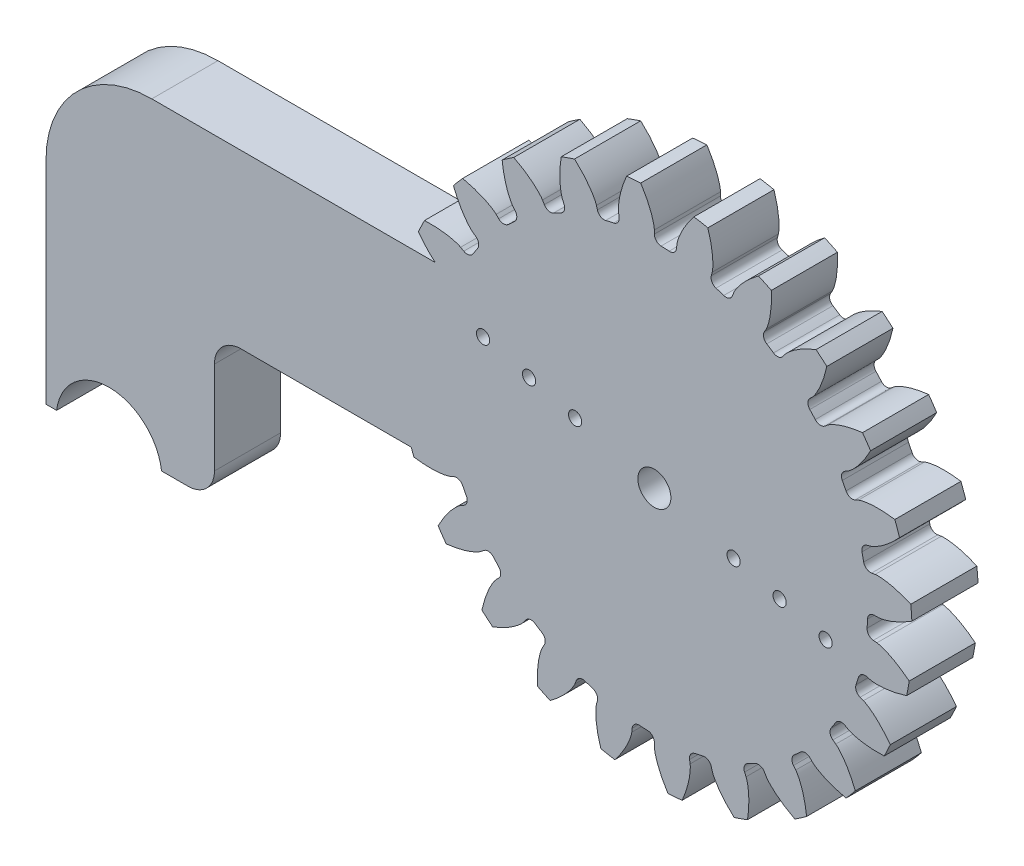
SolidWorks part; units mm, degrees
other "标注1"
sketch "草图12" plane through (-30.0305, -39.4698, -2.5) normal (-0.0916, -0.3639, -0.9269) x (-0.8028, -0.5238, 0.285)
ref_plane "前视基准面" through (0, 0, 0) normal (0, 0, 1) x (1, 0, 0)
ref_plane "上视基准面" through (0, 0, 0) normal (0, 1, 0) x (1, 0, 0)
ref_plane "右视基准面" through (0, 0, 0) normal (1, 0, 0) x (0, 0, -1)
sketch "草图1" plane through (0, 0, 0) normal (0, 0, 1) x (1, 0, 0)
  circle A0 centre (0, 0) radius 19.5
  dimension "D1" = 39
extrude "凸台-拉伸1" add sketch "草图1" along normal mid plane 5
sketch "草图4" plane through (0, 0, 0) normal (0, 0, 1) x (1, 0, 0)
  line L1 (0, 0) -> (23.8901, -1.2086) construction
  line L2 (16.9145, 0) -> (16.125, 0)
  line L3 (16.8281, -1.707) -> (16.0427, -1.6273)
  arc A1 (17.998, 0.2683) -> (17.977, -0.9094) centre (0, 0) cw construction
  arc A3 (23.372, 5.0941) -> (22.7385, -7.4268) centre (0, 0) cw
  arc A4 (16.0427, -1.6273) -> (16.125, 0) centre (0, 0) ccw
  spline S0 degree 4 poles (16.8281, -1.707) (16.8405, -1.7085) (16.8752, -1.7136) (16.9404, -1.7264) (17.0458, -1.7519) (17.1786, -1.7908) (17.3482, -1.8487) (17.545, -1.9264) (17.7579, -2.0215) (17.9853, -2.1355) (18.2084, -2.2583) (18.4269, -2.3892) (18.6409, -2.527) (18.8954, -2.7025) (19.194, -2.9248) (19.5326, -3.2014) (19.9037, -3.5346) (20.2673, -3.8941) (20.6127, -4.264) (20.9467, -4.6555) (21.259, -5.0467) (21.567, -5.4702) (21.843, -5.8697) (22.1332, -6.3351) (22.3619, -6.716) (22.6425, -7.2361) (22.8019, -7.5485) (22.981, -7.9199) (23.0566, -8.0879) (23.1032, -8.1912) knots 0 0 0 0 0 0.005377 0.015084 0.028532 0.04661 0.064855 0.092111 0.119476 0.146842 0.174209 0.201575 0.228941 0.256307 0.307035 0.361767 0.4165 0.471232 0.525964 0.580697 0.635429 0.690161 0.744894 0.799626 0.854358 0.909091 0.954545 1 1 1 1 1 construction
  spline S1 degree 4 poles (16.8281, -1.707) (16.8405, -1.7085) (16.8752, -1.7136) (16.9404, -1.7264) (17.0458, -1.7519) (17.1786, -1.7908) (17.3482, -1.8487) (17.545, -1.9264) (17.7579, -2.0215) (17.9853, -2.1355) (18.2084, -2.2583) (18.4269, -2.3892) (18.6409, -2.527) (18.8954, -2.7025) (19.194, -2.9248) (19.5326, -3.2014) (19.9037, -3.5346) (20.2673, -3.8941) (20.6127, -4.264) (20.9467, -4.6555) (21.259, -5.0467) (21.567, -5.4702) (21.843, -5.8697) (22.1332, -6.3351) (22.3619, -6.716) (22.5816, -7.1233) (22.6862, -7.3236) (22.7386, -7.4268) knots 0 0 0 0 0 0.005377 0.015084 0.028532 0.04661 0.064855 0.092111 0.119476 0.146842 0.174209 0.201575 0.228941 0.256307 0.307035 0.361767 0.4165 0.471232 0.525964 0.580697 0.635429 0.690161 0.744894 0.799626 0.854358 0.909089 0.909089 0.909089 0.909089 0.909089
  spline S2 degree 4 poles (16.9145, 0) (16.927, 0.0003) (16.962, 0.0018) (17.0281, 0.008) (17.1356, 0.0227) (17.2716, 0.0481) (17.4462, 0.0885) (17.6498, 0.1459) (17.8712, 0.2191) (18.109, 0.3096) (18.3433, 0.4092) (18.5739, 0.5174) (18.8007, 0.6329) (19.0717, 0.7818) (19.3912, 0.9728) (19.7559, 1.2138) (20.1588, 1.5079) (20.5568, 1.8288) (20.9378, 2.162) (21.3096, 2.5178) (21.6598, 2.8755) (22.0089, 3.2657) (22.3239, 3.6354) (22.6595, 4.0691) (22.9254, 4.4249) (23.2571, 4.9141) (23.4473, 5.2088) (23.6629, 5.5603) (23.7551, 5.7197) (23.8119, 5.8178) knots 0 0 0 0 0 0.005377 0.015084 0.028532 0.04661 0.064855 0.092111 0.119476 0.146842 0.174209 0.201575 0.228941 0.256307 0.307035 0.361767 0.4165 0.471232 0.525964 0.580697 0.635429 0.690161 0.744894 0.799626 0.854358 0.909091 0.954545 1 1 1 1 1 construction
  spline S3 degree 4 poles (16.9145, 0) (16.927, 0.0003) (16.962, 0.0018) (17.0281, 0.008) (17.1356, 0.0227) (17.2716, 0.0481) (17.4462, 0.0885) (17.6498, 0.1459) (17.8712, 0.2191) (18.109, 0.3096) (18.3433, 0.4092) (18.5739, 0.5174) (18.8007, 0.6329) (19.0717, 0.7818) (19.3912, 0.9728) (19.7559, 1.2138) (20.1588, 1.5079) (20.5568, 1.8288) (20.9378, 2.162) (21.3096, 2.5178) (21.6598, 2.8755) (22.0089, 3.2657) (22.3239, 3.6354) (22.6595, 4.0691) (22.9254, 4.4249) (23.1852, 4.808) (23.3094, 4.9967) (23.372, 5.0941) knots 0 0 0 0 0 0.005377 0.015084 0.028532 0.04661 0.064855 0.092111 0.119476 0.146842 0.174209 0.201575 0.228941 0.256307 0.307035 0.361767 0.4165 0.471232 0.525964 0.580697 0.635429 0.690161 0.744894 0.799626 0.854358 0.909091 0.909091 0.909091 0.909091 0.909091
  dimension "D1" = 18
  dimension "D3" = 32.25
  dimension "D2" = 1.1781
ref_plane "基准面2" through (0, 0, 0) normal (-0.0505, -0.9987, 0) x (0.9987, -0.0505, 0)
extrude "切除-拉伸1" cut sketch "草图4" against normal through all both and the other way through all
fillet "圆角1" radius 0.525 2 edges at (16.0427, -1.6273, 0) (16.125, 0, 0)
pattern_circular "阵列(圆周)1" count 24 over 360 about axis through (0, 0, 2.5) along (0, 0, -1) of "切除-拉伸1", "圆角1"
sketch "草图5" plane through (0, 0, 0) normal (0, 0, 1) x (1, 0, 0)
  line L1 (-3, 0) -> (3, 0)
  line L2 (-3, 0) -> (-3, -10.8)
  line L3 (-3, -10.8) -> (3, -10.8)
  line L4 (3, 0) -> (3, -10.8)
  line L5 (-3, 0) -> (3, -10.8) construction
  line L6 (-3, -10.8) -> (3, 0) construction
  circle A0 centre (0, 0) radius 9
  point P3 (0, -5.4)
  dimension "D1" = 18
  dimension "D2" = 19.8
  dimension "D3" = 6
extrude "切除-拉伸2" [suppressed] cut sketch "草图5" against normal through all both and the other way through all contours A0 L2 L3 L4
sketch "草图6" plane through (0, 0, 2.5) normal (0, 0, 1) x (1, 0, 0)
  circle A0 centre (0, 0) radius 18 construction
  dimension "D1" = 36
sketch "草图7" plane through (0, 0, 2.5) normal (0, 0, 1) x (1, 0, 0)
  circle A0 centre (0, 0) radius 1.25
  dimension "D1" = 2.5
extrude "切除-拉伸3" cut sketch "草图7" against normal blind 10
sketch "草图8" plane through (0, 0, -2.5) normal (0, 0, -1) x (-1, 0, 0)
  circle A0 centre (12.9515, 3.4377) radius 0.5
  circle A1 centre (9.472, 2.5141) radius 0.5
  circle A2 centre (-9.472, -2.5141) radius 0.5
  circle A3 centre (-12.9515, -3.4377) radius 0.5
  dimension "D1" = 1
  dimension "D2" = 1
  dimension "D3" = 1
  dimension "D4" = 1
  dimension "D5" = 9.8
  dimension "D6" = 9.8
  dimension "D7" = 13.4
  dimension "D8" = 22.4236
extrude "切除-拉伸4" cut sketch "草图8" against normal blind 10
sketch "草图10" plane through (0, 0, -2.5) normal (0, 0, -1) x (-1, 0, 0)
  line L4 (0, -18) -> (60.7894, -18) construction
  line L6 (0, 0) -> (60.7894, 0) construction
  line L14 (14, 6.5) -> (14, -6.5)
  line L20 (46, -17.5) -> (45.2, -17.5)
  line L21 (37.2627, -17.5) -> (33.2627, -17.5)
  line L22 (33.2627, -17.5) -> (33.2627, -6.5)
  line L23 (14, -6.5) -> (33.2627, -6.5)
  line L24 (46, 6.5) -> (46, -17.5)
  line L25 (14, 6.5) -> (46, 6.5)
  circle A3 centre (0, 0) radius 18 construction
  arc A4 (45.2, -17.5) -> (37.2627, -17.5) centre (41.2314, -18) ccw
  dimension "D2" = 32
  dimension "D1" = 14
  dimension "D7" = 24
  dimension "D4" = 4
  dimension "D3" = 13
  dimension "D5" = 0.5
  dimension "D6" = 0.8
  dimension "D8" = 4
extrude "凸台-拉伸2" add sketch "草图10" against normal up to surface (5 mm away) up to face at (-12.4515, 3.4377, 2.5)
sketch "草图11" plane through (0, 0, -2.5) normal (0, 0, -1) x (-1, 0, 0)
  circle A0 centre (5.9925, 1.5906) radius 0.5
  circle A1 centre (-5.9925, -1.5906) radius 0.5
extrude "切除-拉伸5" cut sketch "草图11" against normal up to surface (5 mm away) up to face at (0.6253, -0.4313, 2.5)
fillet "圆角2" radius 2 1 edges at (-33.2627, -6.5, 0)
fillet "圆角3" radius 2 1 edges at (-33.2627, -17.5, 0)
fillet "圆角4" radius 8 1 edges at (-46, 6.5, 0)
equation "\"D1@草图1\" = \"da\""
equation "\"D1@凸台-拉伸1\"=\"b\""
equation "\"b\"= 5'齿轮宽度"
equation "\"m\"= 1.5mm'模数"
equation "\"z\"= 24'齿数"
equation "\"x\"= 0'变位系数"
equation "\"pz\"= pi * \"m\"'导程"
equation "\"ha*\"= 1'齿顶高系数"
equation "\"c*\"= 0.25'顶隙系数"
equation "\"d2\"= \"m\" * \"z\"'分度圆"
equation "\"alfa\"= 20'压力角"
equation "\"db\"= \"d2\" * cos ( \"alfa\" )'基圆"
equation "\"df\"= \"d2\" - 2 * ( \"ha*\" + \"c*\" - \"x\" ) * \"m\"'齿根圆"
equation "\"D1@草图4\"=\"d2\"/2"
equation "\"D2@草图4\"=\"pz\"/4"
equation "\"D1@阵列(圆周)1\"=\"z\""
equation "\"D3@草图4\"=\"df\""
equation "\"da\"= \"d2\" + 2 * ( \"ha*\" + \"x\" ) * \"m\"'齿顶圆"
equation "\"c\"= \"m\" * 0.35'齿根圆角"
equation "\"D1@圆角1\"=\"c\""
equation "\"dh\"= 18'内孔直径"
equation "\"h\"= 19.8'槽深"
equation "\"D1@草图5\"=\"dh\""
equation "\"D2@草图5\"=\"h\""
equation "\"k\"= 6'槽宽"
equation "\"D1@草图6\"=\"d2\""
